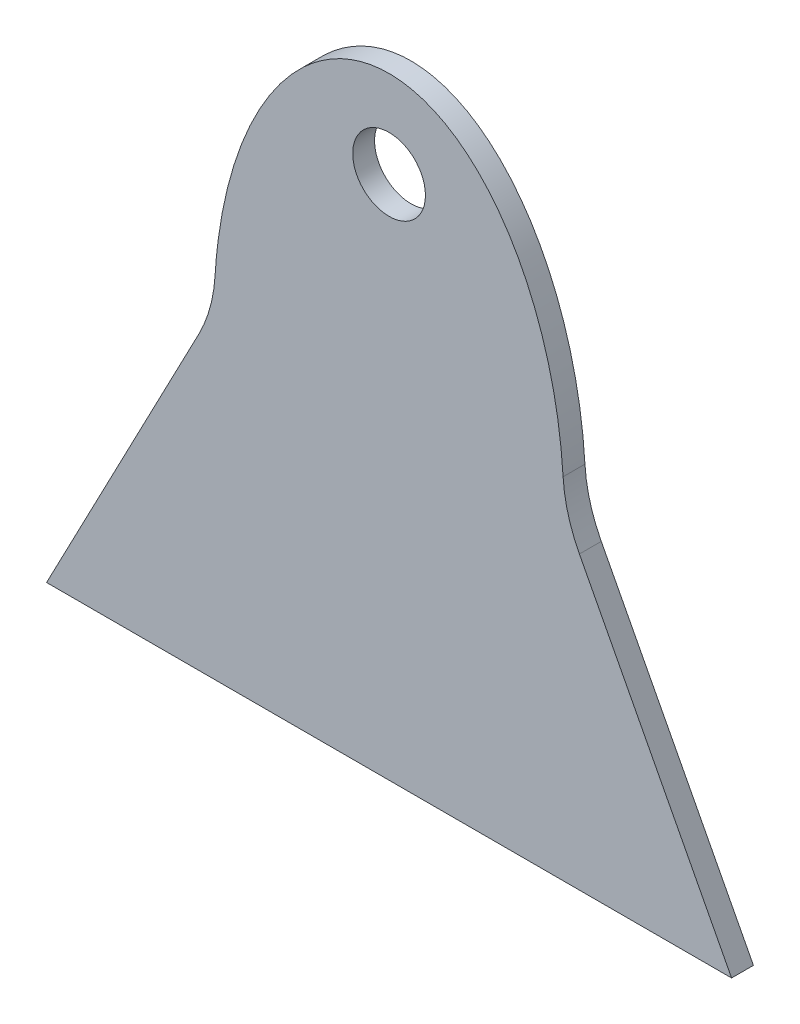
SolidWorks part; units mm, degrees
material "Custom Plastic"
ref_plane "Front Plane" through (0, 0, 0) normal (0, 0, 1) x (1, 0, 0)
ref_plane "Top Plane" through (0, 0, 0) normal (0, 1, 0) x (1, 0, 0)
ref_plane "Right Plane" through (0, 0, 0) normal (1, 0, 0) x (0, 0, -1)
sketch "Sketch1" plane through (0, 0, 0) normal (0, 0, 1) x (1, 0, 0)
  line L0 (-152.4, 0) -> (152.4, 0)
  circle A0 centre (0, 177.8) radius 31.6865
  ellipse E0 centre (0, 0) end of major axis (0, 254) minor radius 152.4 (152.4, 0) -> (-152.4, 0) ccw
  dimension "2.5" = 63.373
  dimension "D1" = 76.2
  dimension "D2" = 152.4
  dimension "D4" = 177.8
extrude "Boss-Extrude1" add sketch "Sketch1" along normal blind 19.05
sketch "Sketch2" plane through (0, 0, 19.05) normal (0, 0, 1) x (1, 0, 0)
  line L0 (-152.4, 0) -> (-298.45, -279.4)
  line L1 (-152.4, 0) -> (152.4, 0)
  line L5 (-152.4, 0) -> (152.4, -279.4) construction
  line L6 (-152.4, -279.4) -> (152.4, 0) construction
  line L8 (0, 0) -> (0, -279.4) construction
  line L10 (152.4, 0) -> (298.45, -279.4)
  line L13 (298.45, -279.4) -> (-298.45, -279.4)
  line L14 (298.45, -279.4) -> (-298.45, -279.4) construction
  point P4 (0, -139.7)
  dimension "D1" = 596.9
extrude "Boss-Extrude2" add sketch "Sketch2" against normal up to surface (19.05 mm away) up to face at (0, 127, 0)
fillet "Fillet1" radius 127 2 edges at (-152.4, 0, 9.525) (152.4, 0, 9.525)
